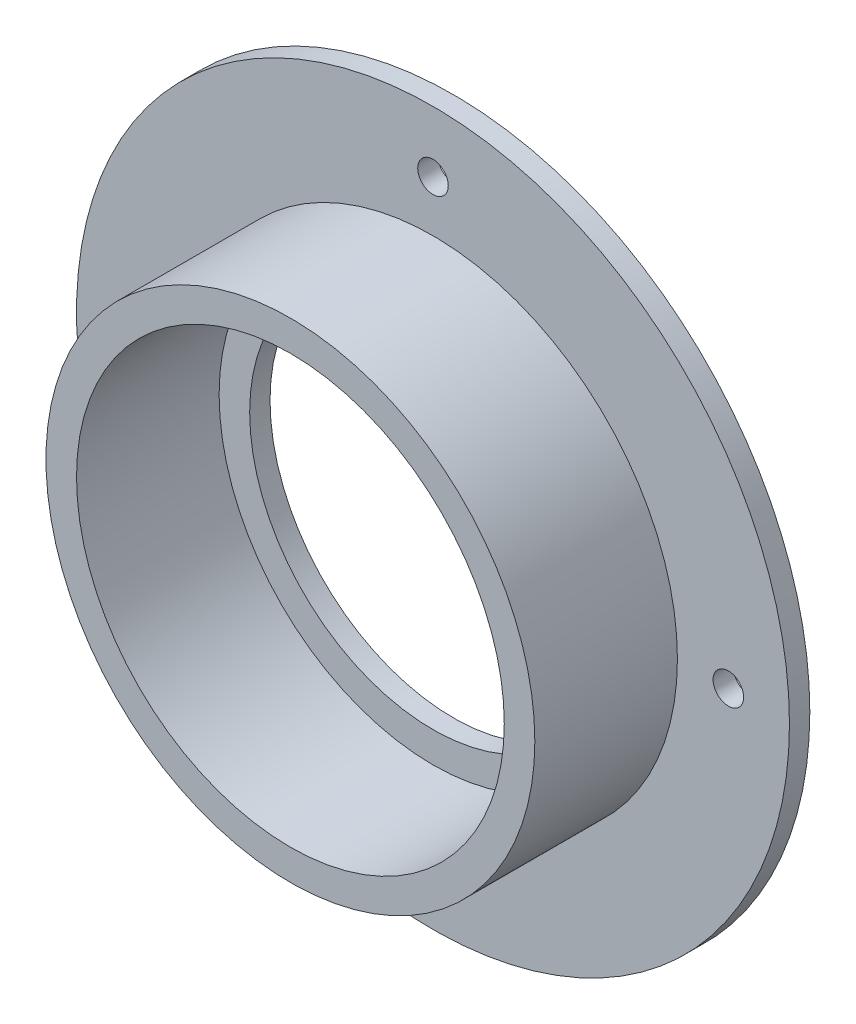
SolidWorks part; units mm, degrees
material "Alloy Steel (SS)"
ref_plane "Front Plane" through (0, 0, 0) normal (0, 0, 1) x (1, 0, 0)
ref_plane "Top Plane" through (0, 0, 0) normal (0, 1, 0) x (1, 0, 0)
ref_plane "Right Plane" through (0, 0, 0) normal (1, 0, 0) x (0, 0, -1)
sketch "Sketch1" plane through (0, 0, 0) normal (0, 0, 1) x (1, 0, 0)
  circle A0 centre (0, 0) radius 35
  dimension "D1" = 70
extrude "Boss-Extrude1" add sketch "Sketch1" along normal blind 2
sketch "Sketch2" plane through (0, 0, 2) normal (0, 0, 1) x (1, 0, 0)
  circle A0 centre (0, 0) radius 24
  circle A1 centre (0, 0) radius 21
  dimension "D1" = 48
  dimension "D2" = 42
extrude "Boss-Extrude2" add sketch "Sketch2" along normal blind 14
sketch "Sketch3" plane through (0, 0, 2) normal (0, 0, 1) x (1, 0, 0)
  circle A0 centre (0, 0) radius 21
extrude "Cut-Extrude1" cut sketch "Sketch3" against normal blind 10
sketch "Sketch4" plane through (0, 0, 0) normal (0, 0, -1) x (-1, 0, 0)
  circle A0 centre (0, 0) radius 29 construction
  circle A1 centre (29, 0) radius 1.5
  circle A2 centre (0, -29) radius 1.5
  circle A3 centre (-29, 0) radius 1.5
  circle A4 centre (0, 29) radius 1.5
  dimension "D1" = 58
  dimension "D2" = 3
  dimension "D3" = 4
extrude "Cut-Extrude2" cut sketch "Sketch4" against normal up to next
sketch "Sketch5" plane through (0, 0, 0) normal (0, 0, -1) x (-1, 0, 0)
  circle A0 centre (0, 0) radius 18
  circle A1 centre (0, 0) radius 21 construction
  circle A2 centre (0, 0) radius 21
  dimension "D1" = 3
extrude "Boss-Extrude3" add sketch "Sketch5" against normal blind 2
